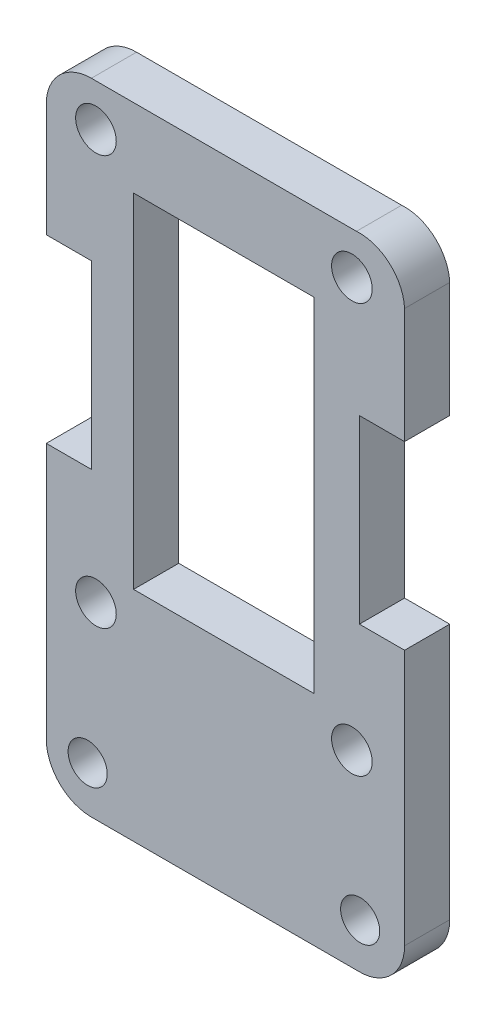
SolidWorks part; units mm, degrees
ref_plane "Front Plane" through (0, 0, 0) normal (0, 0, 1) x (1, 0, 0)
ref_plane "Top Plane" through (0, 0, 0) normal (0, 1, 0) x (1, 0, 0)
ref_plane "Right Plane" through (0, 0, 0) normal (1, 0, 0) x (0, 0, -1)
sketch "Model" plane through (0, 0, 0) normal (0, 0, 1) x (1, 0, 0)
  line L0 (55.6681, 58.3048) -> (55.6681, 35.5048)
  line L1 (58.6687, 41.0048) -> (61.6687, 41.0048)
  line L2 (58.6687, 53.0048) -> (58.6687, 41.0048)
  line L3 (61.6687, 53.0048) -> (58.6687, 53.0048)
  line L5 (61.6687, 53.0048) -> (61.6687, 60.664)
  line L6 (61.6687, 24.0039) -> (61.6687, 41.0048)
  line L7 (41.1672, 33.5047) -> (58.1686, 33.5047) construction
  line L11 (43.6671, 35.5048) -> (55.6681, 35.5048)
  line L12 (43.6671, 58.3048) -> (43.6671, 35.5048)
  line L13 (40.867, 41.0048) -> (37.8668, 41.0048)
  line L14 (40.867, 53.0048) -> (40.867, 41.0048)
  line L15 (37.8668, 53.0048) -> (40.867, 53.0048)
  line L17 (55.6681, 58.3048) -> (43.6671, 58.3048)
  line L18 (40.8628, 63.5066) -> (58.4724, 63.5066)
  line L19 (37.8668, 53.0048) -> (37.8668, 60.6634)
  line L20 (40.7671, 21.0048) -> (58.5682, 21.0048)
  line L21 (37.8668, 41.0048) -> (37.8668, 24.0034)
  line L22 (40.8671, 24.0035) -> (58.6682, 24.0037) construction
  line L23 (41.1672, 60.7069) -> (58.1686, 60.7069) construction
  line L24 (49.6676, 63.5066) -> (49.6676, 21.0048) construction
  circle A0 centre (41.1672, 60.7069) radius 1.3501
  circle A1 centre (58.1686, 60.7069) radius 1.3501
  circle A2 centre (41.1672, 33.5047) radius 1.3501
  circle A3 centre (58.1686, 33.5047) radius 1.3501
  circle A4 centre (40.6173, 24.004) radius 1.3001
  circle A5 centre (58.7188, 24.004) radius 1.3001
  arc A6 (61.6687, 60.664) -> (58.4724, 63.5066) centre (58.6724, 60.5131) ccw
  arc A7 (58.5682, 21.0048) -> (61.6687, 24.0039) centre (58.6682, 24.0037) ccw
  arc A8 (40.8628, 63.5066) -> (37.8668, 60.6634) centre (40.8628, 60.5064) ccw
  arc A9 (37.8668, 24.0034) -> (40.7671, 21.0048) centre (40.8671, 24.0035) ccw
  dimension "D1" = 3
  dimension "D2" = 12
  dimension "D3" = 12.001
  dimension "D4" = 22.8
  dimension "D5" = 14.5
extrude "Boss-Extrude1" add sketch "Model" along normal blind 3
